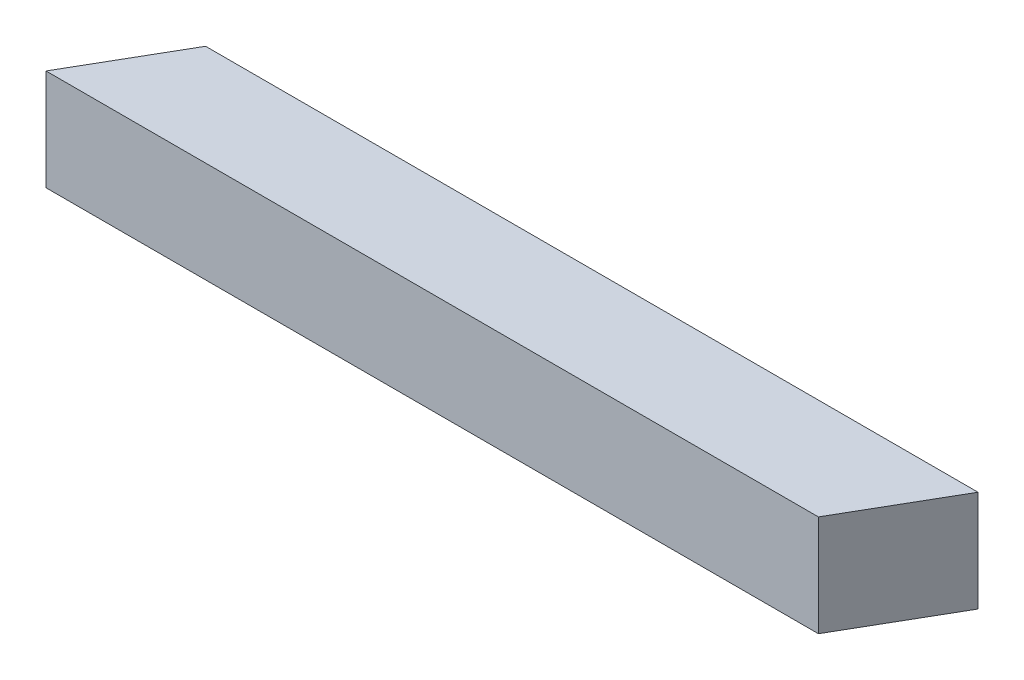
SolidWorks part; units mm, degrees
ref_plane "Front Plane" through (0, 0, 0) normal (0, 0, 1) x (1, 0, 0)
ref_plane "Top Plane" through (0, 0, 0) normal (0, 1, 0) x (1, 0, 0)
ref_plane "Right Plane" through (0, 0, 0) normal (1, 0, 0) x (0, 0, -1)
sketch "Sketch1" plane through (0, 0, 0) normal (0, 1, 0) x (1, 0, 0)
  line L1 (0, 0) -> (76.34, 0) construction
  line L2 (70.5665, -10) -> (82.1135, 10)
  line L4 (0, 27.2438) -> (0, -37.4428) construction
  line L9 (0, -10) -> (70.5665, -10)
  line L10 (82.1135, 10) -> (0, 10)
  line L11 (0, 0) -> (-76.34, 0) construction
  line L12 (0, 10) -> (-70.5665, 10)
  line L13 (-70.5665, 10) -> (-82.1135, -10)
  line L14 (0, -10) -> (-82.1135, -10)
  point P10 (0, -10)
  point P11 (0, -10)
  point P12 (0, 10)
  point P13 (0, 10)
  dimension "D1" = 60
  dimension "D2" = 10
  dimension "D3" = 76.34
  dimension "D4" = 10
  dimension "D6" = 60
extrude "Boss-Extrude1" add sketch "Sketch1" along normal blind 20
